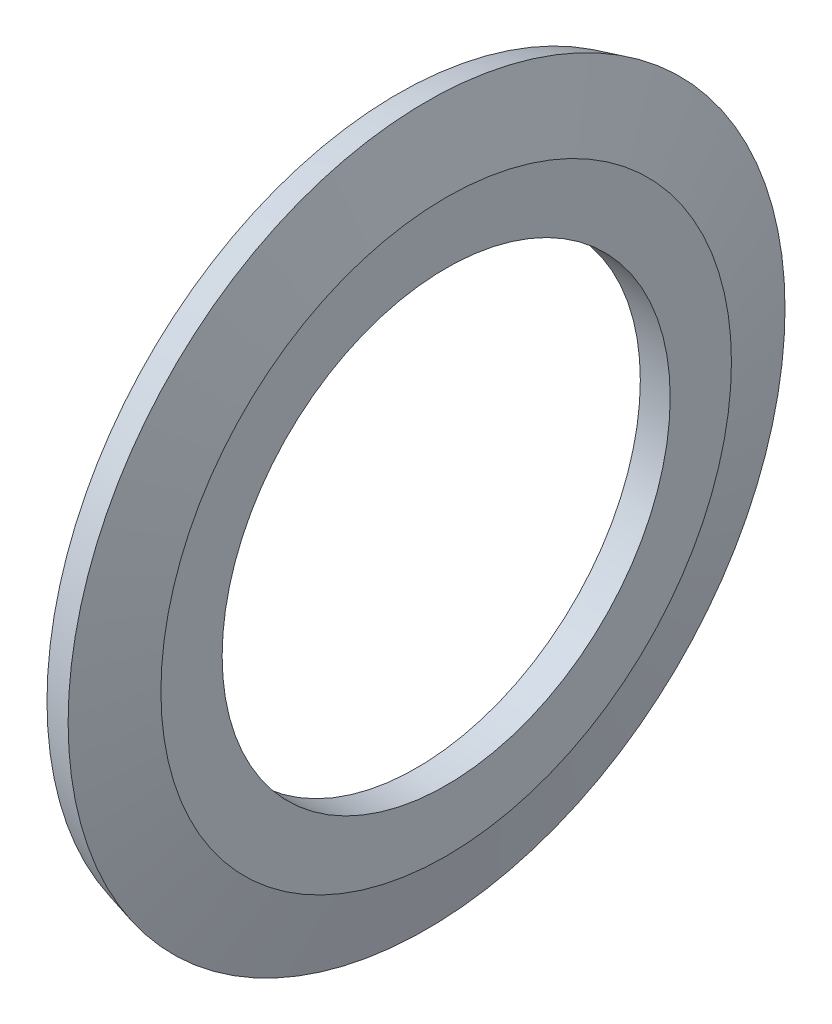
SolidWorks part; units mm, degrees
ref_plane "Front Plane" through (0, 0, 0) normal (0, 0, 1) x (1, 0, 0)
ref_plane "Top Plane" through (0, 0, 0) normal (0, 1, 0) x (1, 0, 0)
ref_plane "Right Plane" through (0, 0, 0) normal (1, 0, 0) x (0, 0, -1)
sketch "Sketch1" plane through (0, 0, 0) normal (0, 0, 1) x (1, 0, 0)
  line L0 (0, 0) -> (1, 0) construction
  line L1 (0, 7.5) -> (0, 9.4183)
  line L2 (0, 9.4183) -> (-0.6224, 11.7412)
  line L3 (1, 7.5) -> (1, 9.55)
  line L4 (1, 9.55) -> (0.3435, 12)
  line L5 (0, 7.5) -> (1, 7.5)
  line L8 (-0.6224, 11.7412) -> (0.3435, 12)
  dimension "D2" = 15
  dimension "F" = 24
  dimension "E" = 15
  dimension "MSM_12" = 1
  dimension "P.D." = 19.1
revolve "Revolve1" add sketch "Sketch1" angle 360 about L0
sketch "Sketch2" [suppressed] plane through (0, 0, 0) normal (0, 0, 1) x (1, 0, 0)
  line L0 (0, 0) -> (0.5753, 0) construction
  line L1 (0, 15.7833) -> (0, -15.7833) construction
  line L3 (0.5753, 17.2412) -> (0, 17.2412)
  line L4 (0.5753, 17.2412) -> (0.5753, 15)
  line L5 (0.5753, 15) -> (0, 15)
  line L6 (0, 17.2412) -> (0, 15)
  line L7 (0.5753, 17.5) -> (0.5753, -17.5) construction
  dimension "FC" = 30
revolve "Cut-Revolve1" [suppressed] cut sketch "Sketch2" angle 360 about L0
